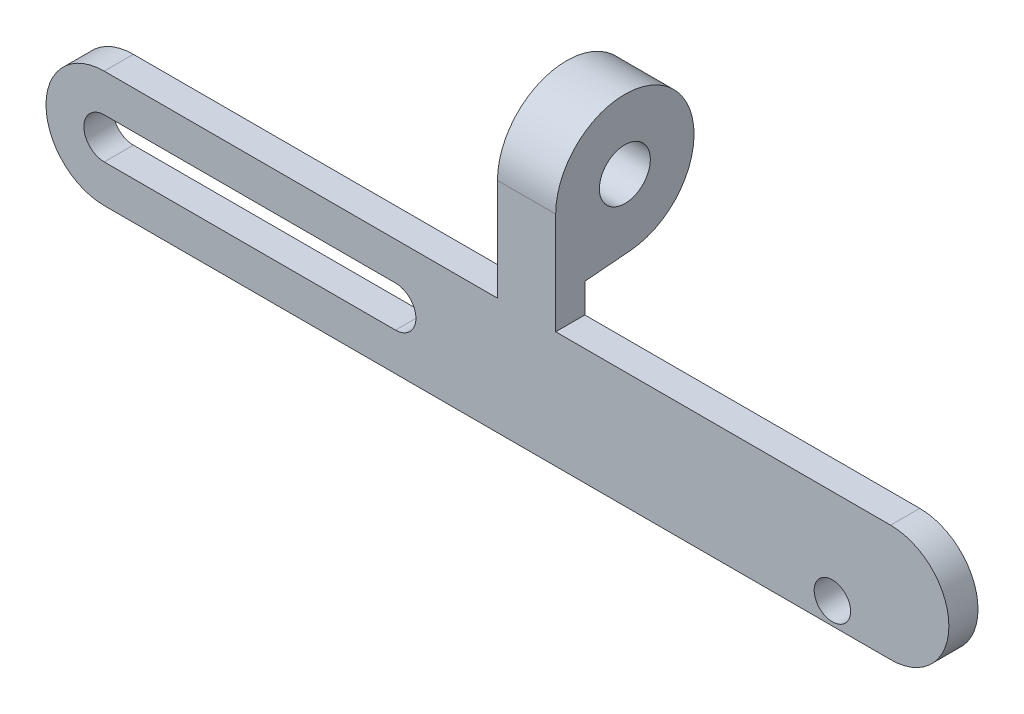
SolidWorks part; units mm, degrees
ref_plane "Plano frontal" through (0, 0, 0) normal (0, 0, 1) x (1, 0, 0)
ref_plane "Plano superior" through (0, 0, 0) normal (0, 1, 0) x (1, 0, 0)
ref_plane "Plano direito" through (0, 0, 0) normal (1, 0, 0) x (0, 0, -1)
sketch "Esboço1" plane through (0, 0, 0) normal (0, 0, 1) x (1, 0, 0)
  line L0 (-27, 0) -> (27, 0) construction
  line L1 (-27, 4) -> (27, 4)
  line L2 (-27, -4) -> (27, -4)
  line L3 (-27, 0) -> (-7, 0) construction
  line L4 (-27, 1.4) -> (-7, 1.4)
  line L5 (-27, -1.4) -> (-7, -1.4)
  arc A0 (-27, 4) -> (-27, -4) centre (-27, 0) ccw
  arc A1 (27, -4) -> (27, 4) centre (27, 0) ccw
  arc A2 (-27, 1.4) -> (-27, -1.4) centre (-27, 0) ccw
  arc A3 (-7, -1.4) -> (-7, 1.4) centre (-7, 0) ccw
  circle A4 centre (23, -2.5) radius 1.25
  point P2 (0, 0)
  point P9 (-17, 0)
  dimension "D2" = 4
  dimension "D3" = 1.4
  dimension "D6" = 2.5
  dimension "D1" = 54
  dimension "D4" = 20
  dimension "D5" = 5
  dimension "D7" = 50
extrude "Ressalto-extrusão1" add sketch "Esboço1" along normal blind 2
sketch "Esboço2" plane through (0, 0, 2) normal (0, 0, 1) x (1, 0, 0)
  circle A0 centre (27, -2.4) radius 0.75
  arc A1 (-27, 1.4) -> (-27, -1.4) centre (-27, 0) ccw construction
  arc A2 (-7, -1.4) -> (-7, 1.4) centre (-7, 0) ccw construction
  point P8 (-5.6, 0)
  dimension "D1" = 1.5
  dimension "D2" = 54
  dimension "D3" = 2.4
extrude "Ressalto-extrusão2" add sketch "Esboço2" against normal blind 5
sketch "Esboço3" plane through (0, 0, 0) normal (1, 0, 0) x (0, 0, -1)
  line L0 (-2, 4) -> (-2, 11)
  line L1 (3.151, 6.267) -> (0, 6)
  line L2 (0, 4) -> (0, 6)
  line L3 (-2, 4) -> (0, 4)
  arc A0 (-2, 11) -> (3.151, 6.267) centre (2.75, 11) cw
  circle A1 centre (2.75, 11) radius 1.75
  dimension "D1" = 3.5
  dimension "D2" = 3
  dimension "D3" = 7
  dimension "D4" = 2
extrude "Ressalto-extrusão3" add sketch "Esboço3" along normal blind 4
